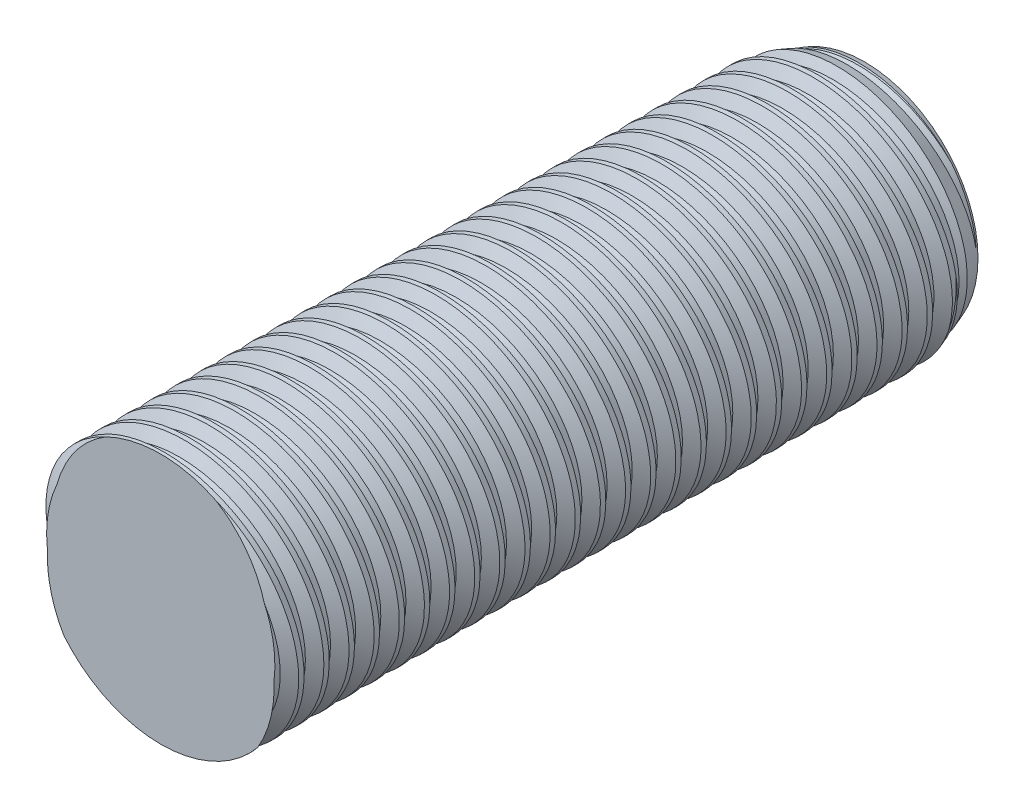
SolidWorks part; units mm, degrees
ref_plane "Front" through (0, 0, 0) normal (0, 0, 1) x (1, 0, 0)
ref_plane "Top" through (0, 0, 0) normal (0, 1, 0) x (1, 0, 0)
ref_plane "Right" through (0, 0, 0) normal (1, 0, 0) x (0, 0, -1)
sketch "Sketch1" plane through (0, 0, 0) normal (1, 0, 0) x (0, 0, -1)
  line L0 (0, 0) -> (-7.9375, 0) construction
  line L1 (0, 0) -> (35.56, 0)
  line L2 (0, 0) -> (0, 6.35)
  line L3 (0, 6.35) -> (35.56, 6.35)
  line L4 (35.56, 0) -> (35.56, 6.35)
  line L5 (0, -6.35) -> (35.56, -6.35) construction
  dimension "D1" = 35.56
  dimension "Thread Dia" = 12.7
  dimension "Length" = 35.56
  dimension "Head Height" = 7.9375
revolve "Revolve1" add sketch "Sketch1" angle 360 about L0
ref_plane "Plane1" through (0, 0, 7.9375) normal (0, 0, 1) x (1, 0, 0)
sketch "Sketch2" plane through (0, 0, 0) normal (1, 0, 0) x (0, 0, -1)
  line L0 (0, 6.35) -> (0, -6.35) construction
  line L1 (0, -6.35) -> (1.27, -6.35) construction
  line L2 (1.27, -6.35) -> (0, 6.35) construction
  line L3 (0, 6.35) -> (0.158, 6.3658) construction
  line L4 (0.158, 6.3658) -> (1.2637, 6.4764)
  line L5 (1.2637, 6.4764) -> (0.9372, 5.7529)
  line L6 (0.9372, 5.7529) -> (0.6213, 5.7213)
  line L7 (0.6213, 5.7213) -> (0.158, 6.3658)
  line L8 (0.7792, 5.7371) -> (0.7108, 6.4211) construction
  line L9 (0, -6.35) -> (35.56, -6.35) construction
  line L10 (0, 6.35) -> (35.56, 6.35) construction
  line L12 (0.7179, 6.35) -> (1.9879, -6.35) construction
  line L13 (0, -0.1353) -> (2.7059, 0.1353) construction
  line L15 (0, 0) -> (0, 6.35) construction
  point P19 (1.3529, 0)
  dimension "D1" = 60
  dimension "Thread Pitch" = 1.27
  dimension "D2" = 0.1588
  dimension "D3" = 0.3175
  dimension "D4" = 1.27
revolve "Cut-Revolve1" cut sketch "Sketch2" angle 360 about L13
sketch "Sketch3" plane through (0, 0, 0) normal (1, 0, 0) x (0, 0, -1)
  line L0 (35.56, 5.7213) -> (33.8326, 6.35)
  line L1 (33.8326, 6.35) -> (35.56, 6.35)
  line L2 (35.56, 6.35) -> (35.56, 5.7213)
  line L3 (0, 6.35) -> (35.56, 6.35) construction
  line L4 (35.56, 0) -> (35.56, 6.35) construction
  line L5 (33.8326, 0) -> (0, 0) construction
  line L6 (33.8326, 6.35) -> (33.8326, -6.35) construction
  line L7 (0, -6.35) -> (35.56, -6.35) construction
  dimension "D1" = 20
  dimension "D2" = 12.7
revolve "Cut-Revolve2" cut sketch "Sketch3" angle 360 about L5
pattern_linear "LPattern1" count 28 spacing 1.27 along (0, 0, -1) of "Cut-Revolve1"
pattern_linear "LPattern2" count 2 spacing 1.27 along (0, 0, 1) of "Cut-Revolve1"
equation "\"D2@Sketch2\"=\"Thread Pitch@Sketch2\"/8"
equation "\"D3@Sketch2\"=\"Thread Pitch@Sketch2\"/4"
equation "\"D4@Sketch2\"=\"Thread Pitch@Sketch2\""
equation "\"D3@LPattern1\"=\"Thread Pitch@Sketch2\""
equation "\"D1@LPattern1\"=\"D1@Sketch1\"/\"Thread Pitch@Sketch2\""
equation "\"D3@LPattern2\"=\"Thread Pitch@Sketch2\""
